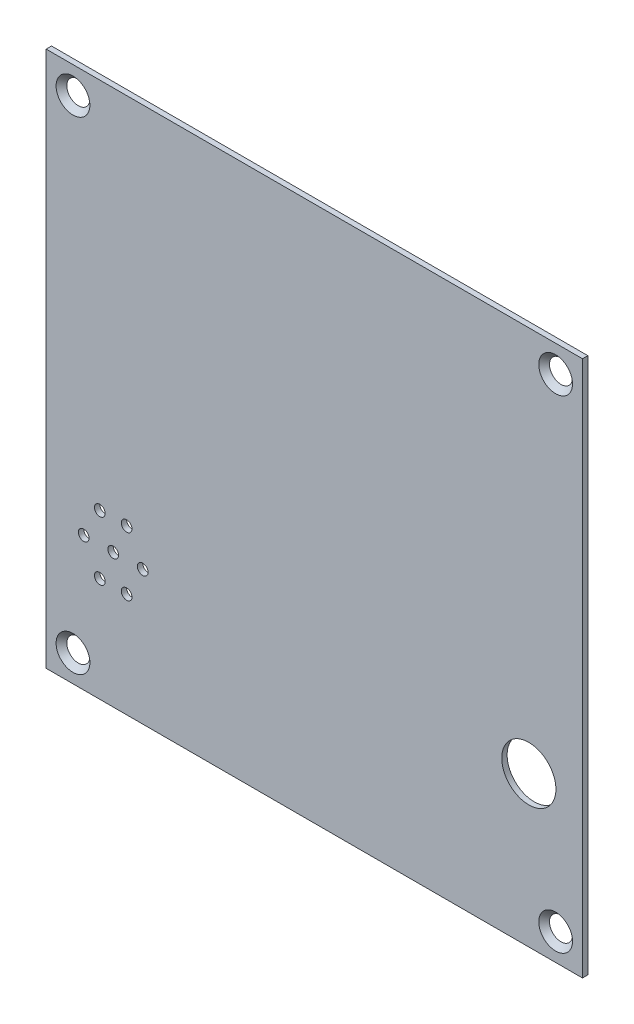
SolidWorks part; units mm, degrees
material "Perspex (TM) Plaque acrylique coulée"
ref_plane "Plan de face" through (0, 0, 0) normal (0, 0, 1) x (1, 0, 0)
ref_plane "Plan de dessus" through (0, 0, 0) normal (0, 1, 0) x (1, 0, 0)
ref_plane "Plan de droite" through (0, 0, 0) normal (1, 0, 0) x (0, 0, -1)
sketch "Esquisse1" plane through (0, 0, 0) normal (0, 0, 1) x (1, 0, 0)
  line L1 (0, 0) -> (100, 0)
  line L2 (0, 0) -> (0, 100)
  line L3 (0, 100) -> (100, 100)
  line L4 (100, 0) -> (100, 100)
  dimension "D1" = 100
  dimension "D2" = 100
extrude "Boss.-Extru.1" add sketch "Esquisse1" along normal blind 1
hole_wizard "Fraisage pour vis à tête fraisée M31" positions "Esquisse3D1" profile "Esquisse3" countersink size "M3" standard "ISO" end condition through all
sketch3d "Esquisse3D1"
  line L0 (100, 100, 1) -> (0, 100, 1) construction
  line L1 (0, 100, 1) -> (0, 0, 1) construction
  line L2 (100, 0, 1) -> (100, 100, 1) construction
  line L3 (0, 0, 1) -> (100, 0, 1) construction
  point P0 (5, 95, 1)
  point P2 (95, 95, 1)
  point P4 (95, 5, 1)
  point P6 (5, 5, 1)
  dimension "D1" = 5
  dimension "D2" = 5
  dimension "D3" = 5
  dimension "D4" = 5
  dimension "D5" = 5
  dimension "D6" = 5
  dimension "D7" = 5
  dimension "D8" = 5
sketch "Esquisse3" plane through (5, 95, 1) normal (1, 0, 0) x (0, -1, 0)
  line L0 (0, 0) -> (0, 1)
  line L1 (0, 1) -> (1.8, 1)
  line L2 (1.8, 1) -> (1.8, 1.35)
  line L3 (1.8, 1.35) -> (3.15, 0)
  line L5 (3.15, 0) -> (0, 0)
  line L6 (-1.8, 1.35) -> (-3.15, 0) construction
  line L11 (0, -6.35) -> (0, 107.95) construction
  dimension "Diamètre du perçage jusqu'au prochain" = 3.6
  dimension "Profondeur du perçage jusqu'au prochain" = 1
  dimension "Diamètre du fraisage entrant" = 6.3
  dimension "Angle du fraisage entrant" = 90
sketch "Esquisse4" plane through (0, 0, 1) normal (0, 0, 1) x (1, 0, 0)
  line L0 (0, 0) -> (100, 0) construction
  line L1 (100, 0) -> (100, 100) construction
  line L2 (0, 100) -> (0, 0) construction
  circle A0 centre (90, 28) radius 5.05
  circle A1 centre (12.5, 25) radius 1
  circle A2 centre (10, 19.5) radius 1
  circle A3 centre (7, 25) radius 1
  circle A4 centre (18, 25) radius 1
  circle A5 centre (10, 30.5) radius 1
  circle A6 centre (15, 30.5) radius 1
  circle A7 centre (15, 19.5) radius 1
  dimension "D1" = 28
  dimension "D3" = 12.5
  dimension "D5" = 18
  dimension "D2" = 10
  dimension "D4" = 25
  dimension "D6" = 7
  dimension "D7" = 30.5
  dimension "D8" = 19.5
  dimension "D9" = 25
  dimension "D10" = 30.5
  dimension "D11" = 19.5
  dimension "D12" = 10
  dimension "D13" = 5
  dimension "D14" = 10
  dimension "D15" = 5
extrude "Enlèv. mat.-Extru.1" cut sketch "Esquisse4" against normal through all
sketch "Esquisse5" plane through (0, 0, 1) normal (0, 0, 1) x (1, 0, 0)
  line L0 (0, 100) -> (0, 0) construction
  line L1 (100, 0) -> (100, 100) construction
  line L2 (0, 0) -> (100, 0) construction
  text T0 "Occupé" font "Century Gothic" height 3.5
  text T1 "Attendez"
  text T2 "Entrez"
  text T3 "Sonnez"
  dimension "D7" = 35
  dimension "D1" = 29
  dimension "D2" = 73
  dimension "D3" = 58
  dimension "D4" = 29
  dimension "D5" = 29
  dimension "D6" = 43
  dimension "D8" = 26
